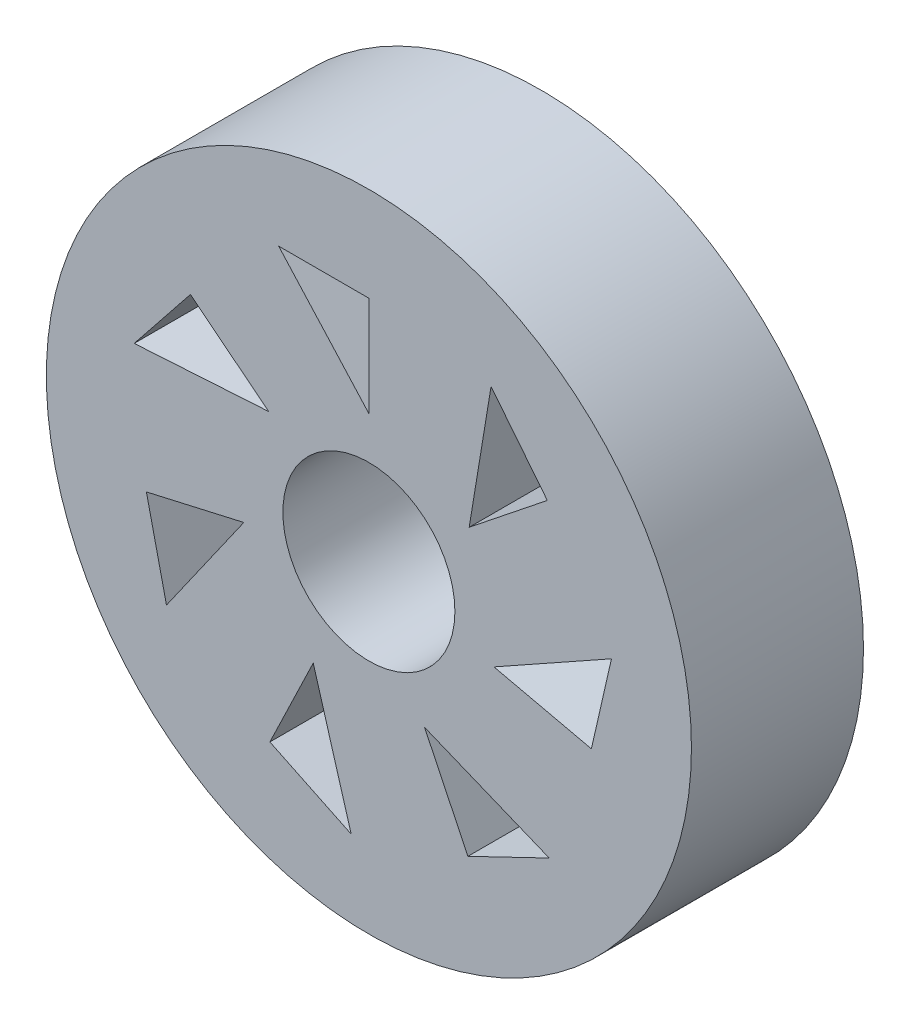
SolidWorks part; units mm, degrees
ref_plane "Front Plane" through (0, 0, 0) normal (0, 0, 1) x (1, 0, 0)
ref_plane "Top Plane" through (0, 0, 0) normal (0, 1, 0) x (1, 0, 0)
ref_plane "Right Plane" through (0, 0, 0) normal (1, 0, 0) x (0, 0, -1)
sketch "Sketch1" plane through (0, 0, 0) normal (0, 0, 1) x (1, 0, 0)
  circle A0 centre (-23.0042, 15.61) radius 19.05
  circle A1 centre (-23.0042, 15.61) radius 5.08
  dimension "D1" = 38.1
  dimension "D2" = 10.16
extrude "Boss-Extrude2" add sketch "Sketch1" along normal blind 10.16
sketch "Sketch3" plane through (0, 0, 10.16) normal (0, 0, 1) x (1, 0, 0)
  line L0 (-23.0042, 23.1867) -> (-28.3345, 29.0881)
  line L1 (-28.3345, 29.0881) -> (-23.0042, 29.0881)
  line L2 (-23.0042, 29.0881) -> (-23.0042, 23.1867)
  line L3 (-12.4666, 24.0135) -> (-17.0805, 20.334)
  line L4 (-15.7899, 28.1808) -> (-12.4666, 24.0135)
  line L5 (-17.0805, 20.334) -> (-15.7899, 28.1808)
  line L6 (-9.864, 12.6108) -> (-15.6175, 13.924)
  line L7 (-8.6779, 17.8074) -> (-9.864, 12.6108)
  line L8 (-15.6175, 13.924) -> (-8.6779, 17.8074)
  line L9 (-17.1563, 3.4666) -> (-19.7168, 8.7836)
  line L10 (-12.3539, 5.7793) -> (-17.1563, 3.4666)
  line L11 (-19.7168, 8.7836) -> (-12.3539, 5.7793)
  line L12 (-28.8522, 3.4666) -> (-26.2916, 8.7836)
  line L13 (-24.0498, 1.1539) -> (-28.8522, 3.4666)
  line L14 (-26.2916, 8.7836) -> (-24.0498, 1.1539)
  line L15 (-36.1444, 12.6108) -> (-30.3909, 13.924)
  line L16 (-34.9583, 7.4142) -> (-36.1444, 12.6108)
  line L17 (-30.3909, 13.924) -> (-34.9583, 7.4142)
  line L18 (-33.5418, 24.0135) -> (-28.9279, 20.334)
  line L19 (-36.8652, 19.8461) -> (-33.5418, 24.0135)
  line L20 (-28.9279, 20.334) -> (-36.8652, 19.8461)
  point P24 (-23.0042, 15.61)
  dimension "D1" = 7
extrude "Cut-Extrude2" cut sketch "Sketch3" against normal blind 10.16
